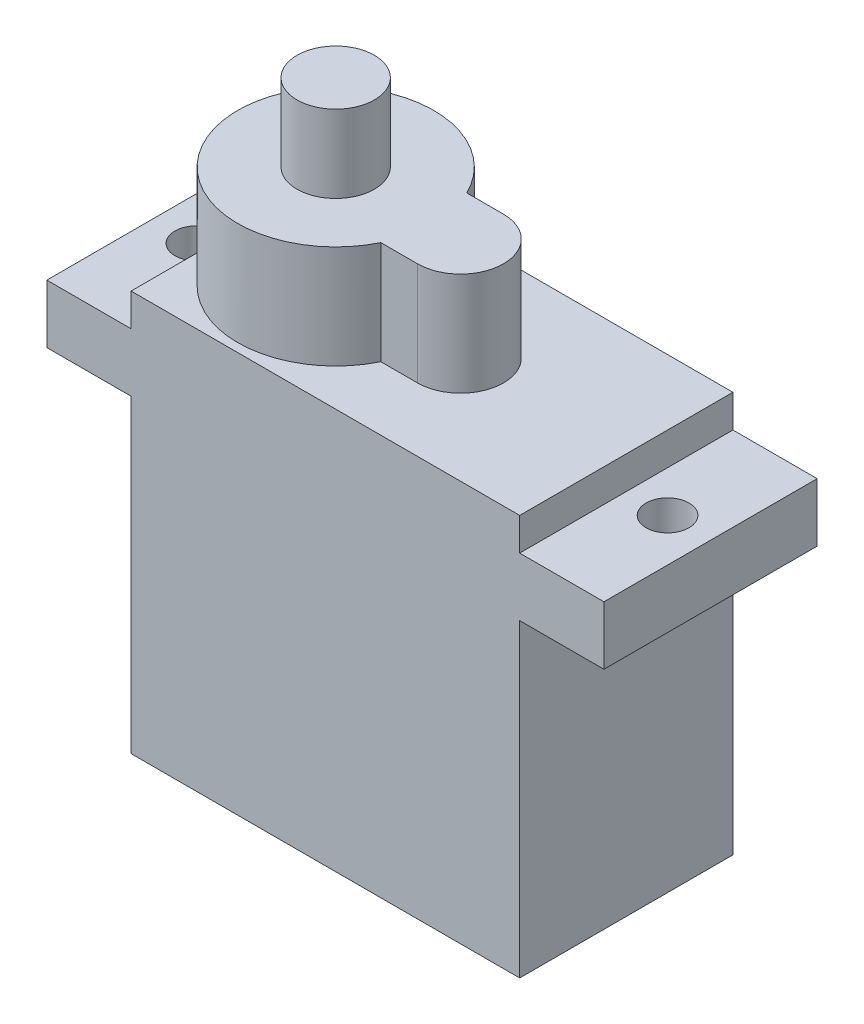
SolidWorks part; units mm, degrees
ref_plane "前视基准面" through (0, 0, 0) normal (0, 0, 1) x (1, 0, 0)
ref_plane "上视基准面" through (0, 0, 0) normal (0, 1, 0) x (1, 0, 0)
ref_plane "右视基准面" through (0, 0, 0) normal (1, 0, 0) x (0, 0, -1)
sketch "草图1" plane through (0, 0, 0) normal (0, 1, 0) x (1, 0, 0)
  line L1 (-11.3, 6.2) -> (11.3, 6.2)
  line L2 (-11.3, 6.2) -> (-11.3, -6.2)
  line L3 (-11.3, -6.2) -> (11.3, -6.2)
  line L4 (11.3, 6.2) -> (11.3, -6.2)
  line L5 (-11.3, 6.2) -> (11.3, -6.2) construction
  line L6 (-11.3, -6.2) -> (11.3, 6.2) construction
  point P0 (0, 0)
  dimension "D1" = 12.4
  dimension "D2" = 22.6
extrude "凸台-拉伸1" add sketch "草图1" along normal blind 18
sketch "草图2" plane through (0, 18, 0) normal (0, 1, 0) x (1, 0, 0)
  line L0 (0, 9.3532) -> (0, -13.0576) construction
  line L1 (-16.2, 6.2) -> (16.2, 6.2)
  line L2 (-16.2, 6.2) -> (-16.2, -6.2)
  line L3 (-16.2, -6.2) -> (16.2, -6.2)
  line L4 (16.2, 6.2) -> (16.2, -6.2)
  line L5 (-18.4217, 0) -> (0, 0) construction
  circle A0 centre (-13.7, 0) radius 1.25
  circle A1 centre (13.7, 0) radius 1.25
  dimension "D2" = 2.5
  dimension "D3" = 2.5
  dimension "D1" = 32.4
extrude "凸台-拉伸2" add sketch "草图2" along normal blind 3.4
sketch "草图3" plane through (0, 21.4, 0) normal (0, 1, 0) x (1, 0, 0)
  line L4 (11.3, -6.2) -> (11.3, 6.2)
  line L5 (-11.3, -6.2) -> (11.3, -6.2)
  line L6 (-11.3, 6.2) -> (-11.3, -6.2)
  line L7 (11.3, 6.2) -> (-11.3, 6.2)
  line L8 (11.3, -6.2) -> (11.3, 6.2)
  line L9 (-11.3, -6.2) -> (11.3, -6.2)
  line L10 (-11.3, 6.2) -> (-11.3, -6.2)
  line L11 (11.3, 6.2) -> (-11.3, 6.2)
  dimension "D1" = 0
extrude "凸台-拉伸3" add sketch "草图3" along normal blind 1.9
sketch "草图4" plane through (0, 23.3, 0) normal (0, 1, 0) x (1, 0, 0)
  line L0 (-11.3, 6.2) -> (-11.3, -6.2) construction
  line L1 (1.6595, 2.5) -> (-0.4775, 2.5)
  line L3 (-0.4775, -2.5) -> (1.6595, -2.5)
  arc A0 (-0.4775, 2.5) -> (-0.4775, -2.5) centre (-5.6, 0) ccw
  arc A1 (1.6595, -2.5) -> (1.6595, 2.5) centre (1.6595, 0) ccw
  dimension "D1" = 11.4
  dimension "D2" = 5
extrude "凸台-拉伸4" add sketch "草图4" along normal blind 6
sketch "草图5" plane through (0, 29.3, 0) normal (0, 1, 0) x (1, 0, 0)
  circle A0 centre (-5.6, 0) radius 2.25
  dimension "D1" = 4.5
extrude "凸台-拉伸5" add sketch "草图5" along normal blind 4.5
